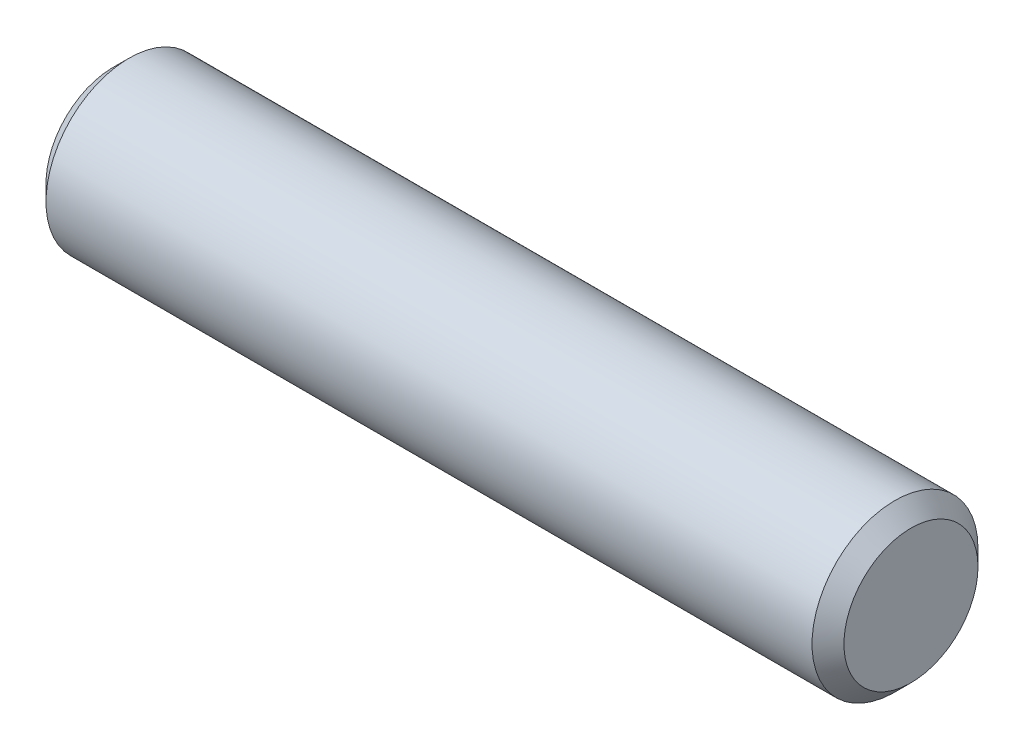
SolidWorks part; units mm, degrees
material "Plain Carbon Steel"
ref_plane "Front Plane" through (0, 0, 0) normal (0, 0, 1) x (1, 0, 0)
ref_plane "Top Plane" through (0, 0, 0) normal (0, 1, 0) x (1, 0, 0)
ref_plane "Right Plane" through (0, 0, 0) normal (1, 0, 0) x (0, 0, -1)
sketch "Sketch1" plane through (0, 0, 0) normal (1, 0, 0) x (0, 0, -1)
  circle A0 centre (0, 0) radius 7.9248
  dimension "D1" = 15.8496
extrude "Boss-Extrude1" add sketch "Sketch1" along normal mid plane 76.2
chamfer "Chamfer1" distance 1.524 angle 45 1 edges at (38.1, 0, -7.9248)
chamfer "Chamfer2" distance 1.524 angle 45 1 edges at (-38.1, 0, -7.9248)
